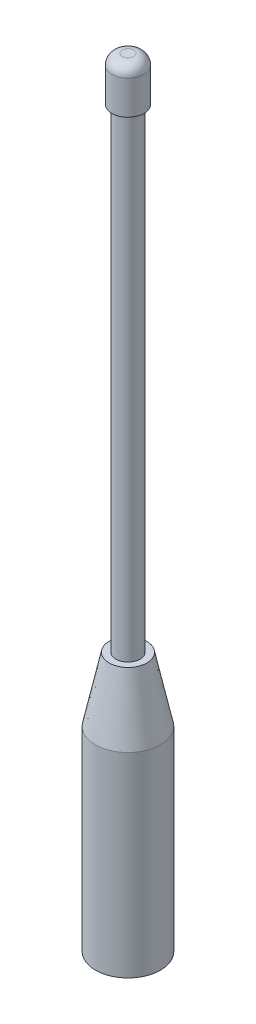
SolidWorks part; units mm, degrees
ref_plane "Front Plane" through (0, 0, 0) normal (0, 0, 1) x (1, 0, 0)
ref_plane "Top Plane" through (0, 0, 0) normal (0, 1, 0) x (1, 0, 0)
ref_plane "Right Plane" through (0, 0, 0) normal (1, 0, 0) x (0, 0, -1)
sketch "Sketch1" plane through (0, 0, 0) normal (0, 1, 0) x (1, 0, 0)
  circle A0 centre (0, 0) radius 2.3813
  dimension "D1" = 4.7625
extrude "Boss-Extrude1" add sketch "Sketch1" along normal blind 152.4
sketch "Sketch2" plane through (0, 0, 0) normal (0, 1, 0) x (1, 0, 0)
  circle A0 centre (0, 0) radius 6.35
  dimension "D1" = 12.7
extrude "Boss-Extrude2" add sketch "Sketch2" along normal blind 50.8
chamfer "Chamfer1" distance 12.54 angle 12 1 edges at (0, 50.8, 6.35)
sketch "Sketch3" plane through (0, 152.4, 0) normal (0, 1, 0) x (1, 0, 0)
  circle A0 centre (0, 0) radius 3.1433
  circle A1 centre (0, 0) radius 2.3813 construction
  dimension "D1" = 0.762
extrude "Boss-Extrude3" add sketch "Sketch3" against normal blind 8.636
fillet "Fillet1" radius 2.032 1 edges at (0, 152.4, 3.1433)
